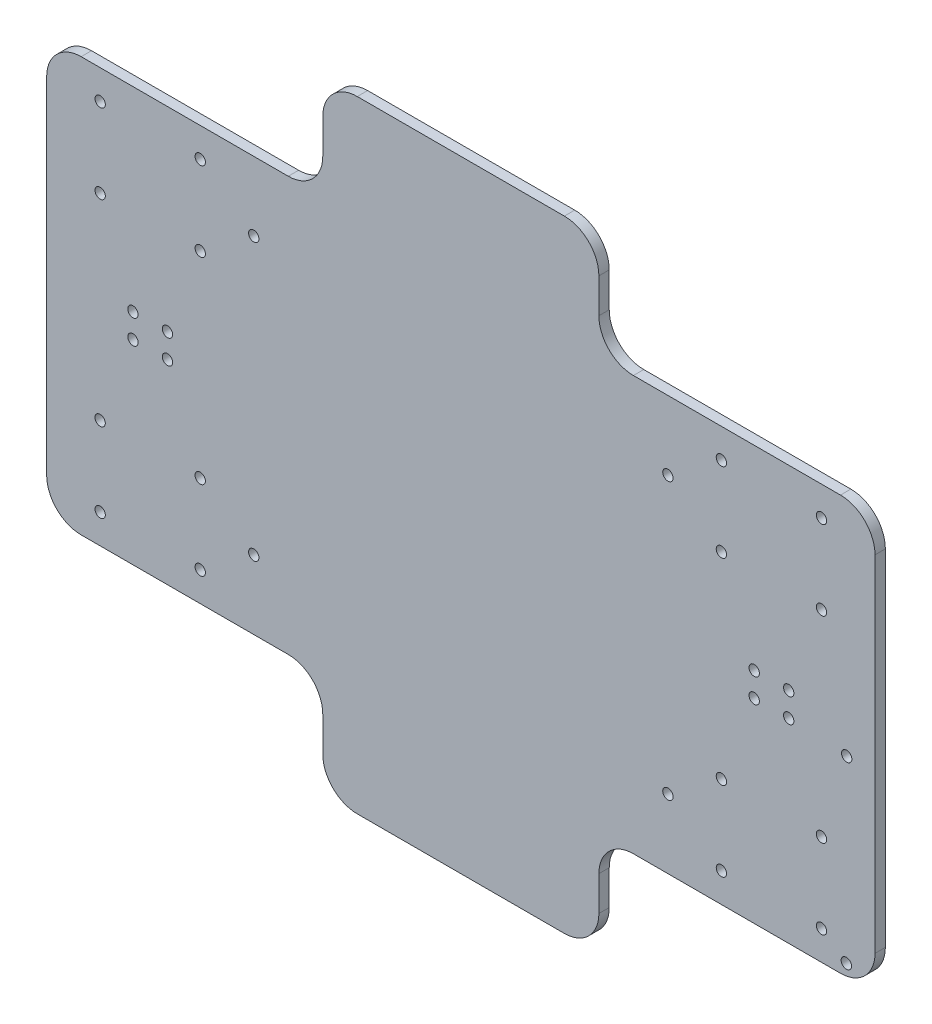
SolidWorks part; units mm, degrees
ref_plane "前基準面" through (0, 0, 0) normal (0, 0, 1) x (1, 0, 0)
ref_plane "上基準面" through (0, 0, 0) normal (0, 1, 0) x (1, 0, 0)
ref_plane "右基準面" through (0, 0, 0) normal (1, 0, 0) x (0, 0, -1)
sketch "草圖1" plane through (0, 0, 0) normal (0, 0, 1) x (1, 0, 0)
  line L0 (80, 0) -> (80, 30)
  line L1 (80, 0) -> (160, 0)
  line L2 (0, 30) -> (0, 150)
  line L3 (80, 180) -> (160, 180)
  line L5 (80, 30) -> (0, 30)
  line L6 (240, 150) -> (240, 30)
  line L7 (80, 180) -> (80, 150)
  line L8 (80, 150) -> (0, 150)
  line L10 (160, 180) -> (160, 150)
  line L11 (160, 150) -> (240, 150)
  line L12 (160, 0) -> (160, 30)
  line L13 (160, 30) -> (240, 30)
  circle A0 centre (15.5, 61.5) radius 1.5
  circle A1 centre (44.5, 61.5) radius 1.5
  circle A2 centre (44.5, 38.5) radius 1.5
  circle A3 centre (15.5, 38.5) radius 1.5
  circle A12 centre (44.5, 141.5) radius 1.5
  circle A13 centre (15.5, 141.5) radius 1.5
  circle A14 centre (15.5, 118.5) radius 1.5
  circle A15 centre (44.5, 118.5) radius 1.5
  circle A16 centre (35, 86.5) radius 1.5
  circle A17 centre (25, 86.5) radius 1.5
  circle A18 centre (60, 50) radius 1.5
  circle A19 centre (25, 93.5) radius 1.5
  circle A20 centre (35, 93.5) radius 1.5
  circle A21 centre (60, 130) radius 1.5
  circle A28 centre (180, 130) radius 1.5
  circle A29 centre (205, 93.5) radius 1.5
  circle A30 centre (215, 93.5) radius 1.5
  circle A31 centre (180, 50) radius 1.5
  circle A32 centre (215, 86.5) radius 1.5
  circle A33 centre (205, 86.5) radius 1.5
  circle A34 centre (195.5, 118.5) radius 1.5
  circle A35 centre (224.5, 118.5) radius 1.5
  circle A36 centre (224.5, 141.5) radius 1.5
  circle A37 centre (195.5, 141.5) radius 1.5
  circle A38 centre (224.5, 38.5) radius 1.5
  circle A39 centre (195.5, 38.5) radius 1.5
  circle A40 centre (195.5, 61.5) radius 1.5
  circle A41 centre (224.5, 61.5) radius 1.5
  point P18 (60, 0)
  point P49 (80, 0)
  dimension "D4" = 3
  dimension "D5" = 3
  dimension "D8" = 3
  dimension "D9" = 3
  dimension "D10" = 3
  dimension "D11" = 3
  dimension "D18" = 3
extrude "填料-伸長1" add sketch "草圖1" along normal blind 3
fillet "圓角1" radius 10 12 edges at (240, 150, 1.5) (160, 150, 1.5) (160, 180, 1.5) (80, 180, 1.5) (80, 150, 1.5) (0, 150, 1.5) (0, 30, 1.5) (80, 30, 1.5) (80, 0, 1.5) (160, 0, 1.5) (160, 30, 1.5) (240, 30, 1.5)
sketch "草圖2" plane through (0, 0, 3) normal (0, 0, 1) x (1, 0, 0)
  line L0 (240, 40) -> (240, 140) construction
  line L1 (170, 30) -> (230, 30) construction
  circle A0 centre (231.8017, 85.38) radius 1.5
  circle A1 centre (231.7, 33.38) radius 1.5
  point P0 (231.7, 33.38)
  point P1 (231.8017, 85.38)
  dimension "D1" = 8.3
  dimension "D2" = 3.38
  dimension "D3" = 52
extrude "除料-伸長1" cut sketch "草圖2" against normal blind 10
